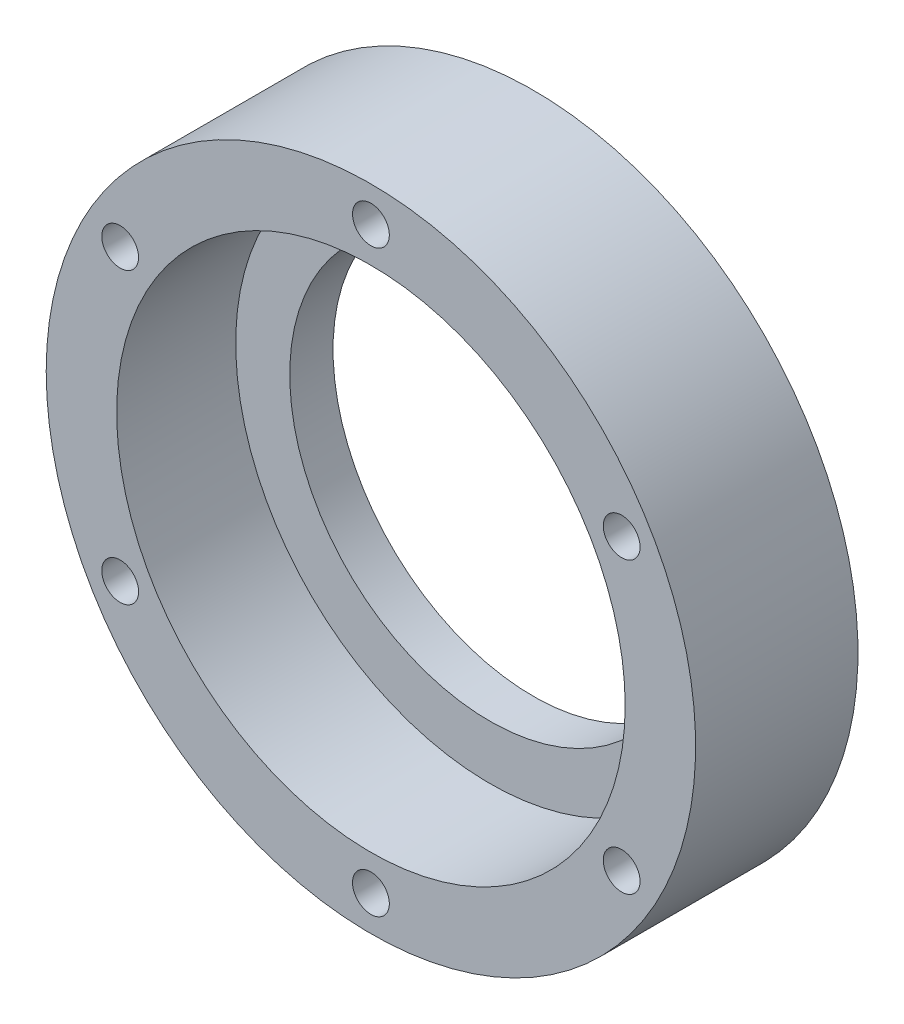
SolidWorks part; units mm, degrees
ref_plane "Front Plane" through (0, 0, 0) normal (0, 0, 1) x (1, 0, 0)
ref_plane "Top Plane" through (0, 0, 0) normal (0, 1, 0) x (1, 0, 0)
ref_plane "Right Plane" through (0, 0, 0) normal (1, 0, 0) x (0, 0, -1)
ref_plane "Plane1" through (0, 0, 0) normal (0, -1, 0) x (1, 0, 0)
sketch "Sketch1" plane through (0, 0, 0) normal (0, -1, 0) x (1, 0, 0)
  line L0 (30, 15) -> (0, 15)
  line L1 (0, 15) -> (0, 0)
  line L2 (0, 0) -> (30, 0)
  line L3 (30, 0) -> (30, 15)
  line L4 (0, 15) -> (0, 0) construction
revolve "Revolve1" add sketch "Sketch1" angle 360 about L4
hole_wizard "#4 Clearance Hole1" positions "Sketch3" profile "Sketch2" hole size "#4" standard "ANSI Inch"
sketch "Sketch3" plane through (0, 0, 0) normal (0, 0, -1) x (-1, 0, 0)
  point P0 (-23.1662, -13.375)
  point P1 (-23.1662, 13.375)
  point P2 (0, 26.75)
  point P3 (23.1662, -13.375)
  point P4 (0, -26.75)
  point P5 (23.1662, 13.375)
sketch "Sketch2" plane through (23.1662, -13.375, 0) normal (1, 0, 0) x (0, 1, 0)
  line L0 (0, 0) -> (0, 15)
  line L1 (0, 15) -> (1.7, 15)
  line L2 (1.7, 15) -> (1.7, 0)
  line L5 (1.7, 0) -> (0, 0)
  line L11 (0, -6.35) -> (0, 107.95) construction
  dimension "Thru Hole Dia." = 3.4
  dimension "Thru Hole Depth" = 15
hole_wizard "Hole1" positions "Sketch5" profile "Sketch4" legacy
sketch "Sketch5" plane through (0, 0, 15) normal (0, 0, 1) x (1, 0, 0)
  point P0 (0, 0)
sketch "Sketch4" plane through (0, 0, 15) normal (1, 0, 0) x (0, -1, 0)
  line L0 (0, 0) -> (0, 15)
  line L1 (0, 15) -> (18.5, 15)
  line L2 (18.5, 15) -> (18.5, 11)
  line L3 (18.5, 11) -> (23.4912, 11)
  line L4 (23.4912, 11) -> (23.4912, 0)
  line L5 (23.4912, 0) -> (0, 0)
  line L6 (0, 110) -> (0, -10) construction
  dimension "Diameter" = 37
  dimension "Depth" = 15
  dimension "C-Bore Diameter" = 46.9824
  dimension "C-Bore Depth" = 11
chamfer "Chamfer1" distance 1.45 angle 45 6 edges at (-24.8662, -13.375, 0) (-24.8662, 13.375, 0) (-1.7, -26.75, 0) (21.4662, 13.375, 0) (21.4662, -13.375, 0) (-1.7, 26.75, 0)
